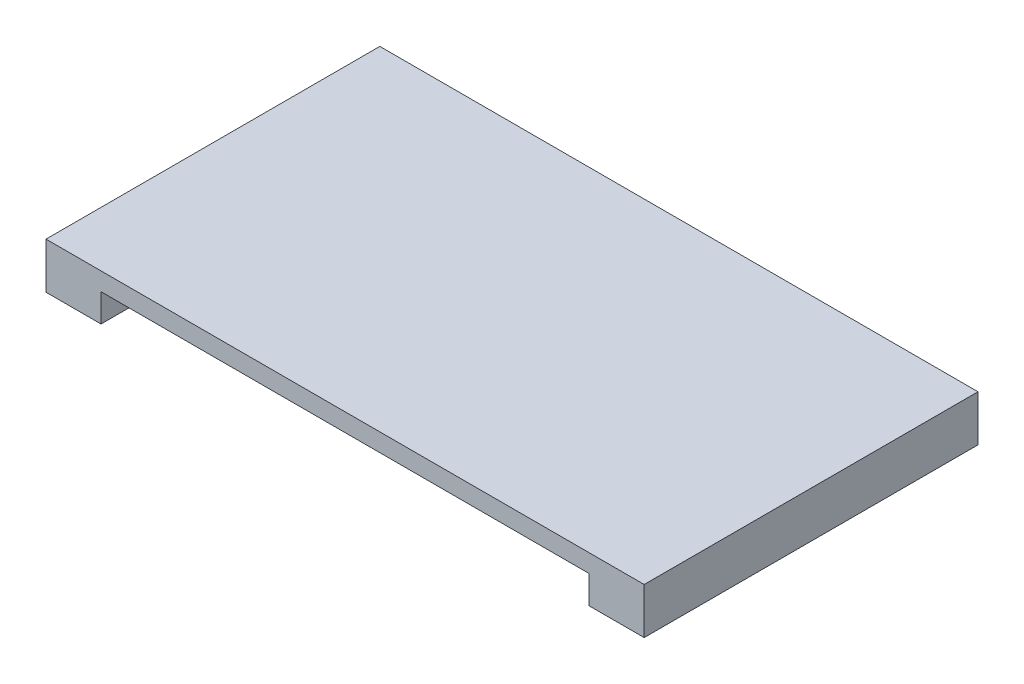
SolidWorks part; units mm, degrees
ref_plane "Front Plane" through (0, 0, 0) normal (0, 0, 1) x (1, 0, 0)
ref_plane "Top Plane" through (0, 0, 0) normal (0, 1, 0) x (1, 0, 0)
ref_plane "Right Plane" through (0, 0, 0) normal (1, 0, 0) x (0, 0, -1)
sketch "Sketch1" plane through (0, 0, 0) normal (0, 1, 0) x (1, 0, 0)
  line L5 (-16.575, -9.25) -> (16.575, -9.25)
  line L6 (-16.575, -9.25) -> (-16.575, 9.25)
  line L7 (-16.575, 9.25) -> (16.575, 9.25)
  line L8 (16.575, -9.25) -> (16.575, 9.25)
  line L9 (-16.575, -9.25) -> (16.575, 9.25) construction
  line L10 (-16.575, 9.25) -> (16.575, -9.25) construction
  point P0 (0, 0)
  dimension "D1" = 33.15
  dimension "D2" = 18.5
extrude "Boss-Extrude1" add sketch "Sketch1" along normal blind 2.55
sketch "Sketch2" plane through (0, 0, 0) normal (0, -1, 0) x (1, 0, 0)
  line L0 (-16.575, 9.25) -> (16.575, 9.25) construction
  line L1 (-13.525, 9.25) -> (13.525, 9.25)
  line L2 (-13.525, 9.25) -> (-13.525, -9.25)
  line L3 (-13.525, -9.25) -> (13.525, -9.25)
  line L4 (13.525, 9.25) -> (13.525, -9.25)
  line L5 (-13.525, 9.25) -> (13.525, -9.25) construction
  line L6 (-13.525, -9.25) -> (13.525, 9.25) construction
  line L7 (16.575, -9.25) -> (-16.575, -9.25) construction
  line L8 (-16.575, -9.25) -> (-16.575, 9.25) construction
  line L9 (16.575, 9.25) -> (16.575, -9.25) construction
  point P4 (0, 0)
  dimension "D1" = 3.05
  dimension "D2" = 3.05
extrude "Cut-Extrude1" cut sketch "Sketch2" against normal blind 1.55
